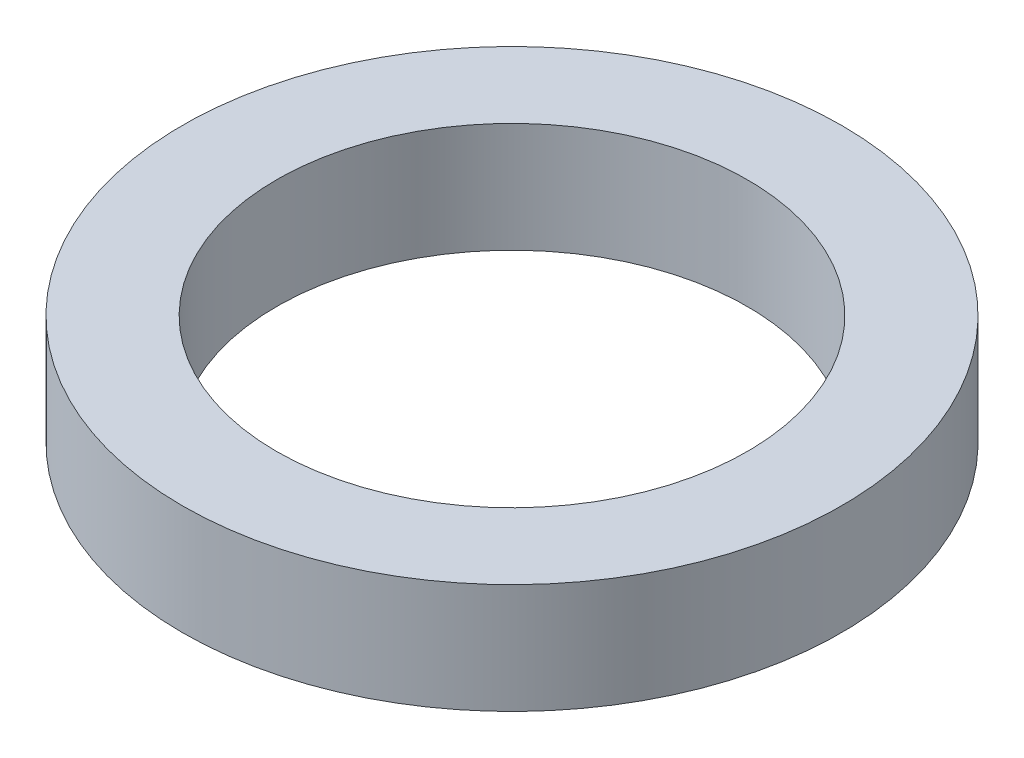
SolidWorks part; units mm, degrees
ref_plane "Front Plane" through (0, 0, 0) normal (0, 0, 1) x (1, 0, 0)
ref_plane "Top Plane" through (0, 0, 0) normal (0, 1, 0) x (1, 0, 0)
ref_plane "Right Plane" through (0, 0, 0) normal (1, 0, 0) x (0, 0, -1)
sketch "Sketch1" plane through (0, 0, 0) normal (0, 1, 0) x (1, 0, 0)
  circle A0 centre (0, 0) radius 15
  circle A1 centre (0, 0) radius 21
  dimension "D1" = 30
  dimension "D2" = 42
extrude "Boss-Extrude1" add sketch "Sketch1" along normal blind 7
